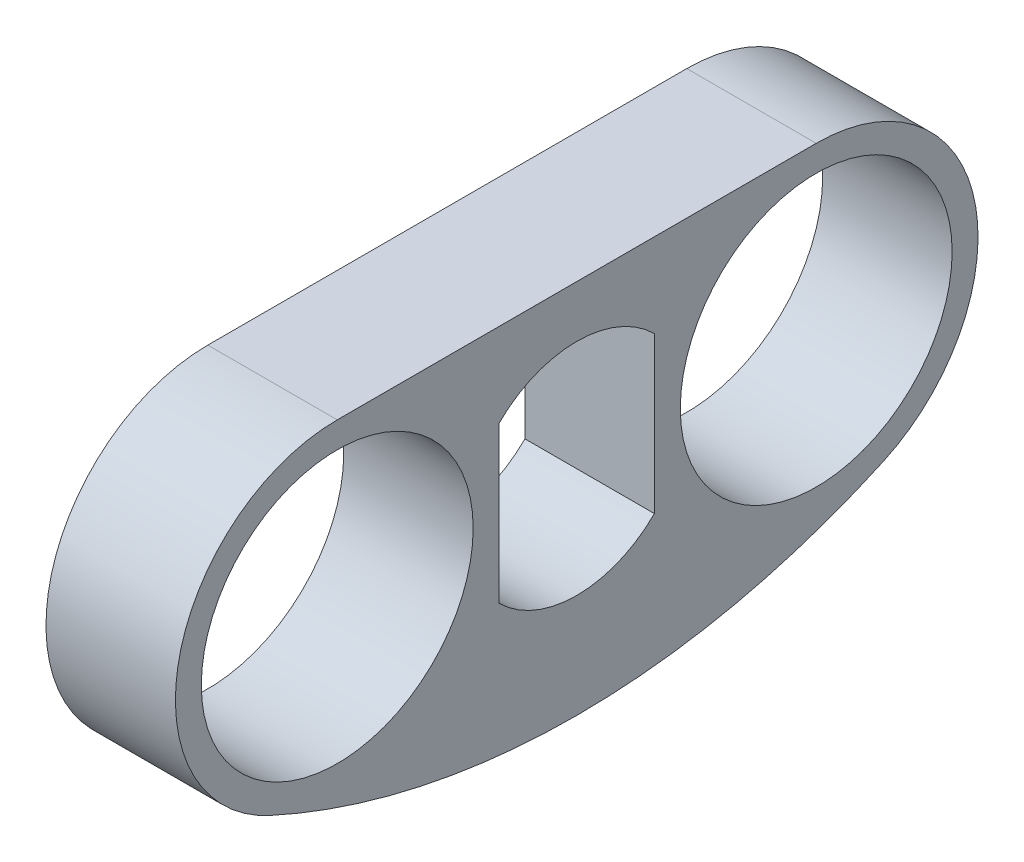
SolidWorks part; units mm, degrees
ref_plane "Alzado" through (0, 0, 0) normal (0, 0, 1) x (1, 0, 0)
ref_plane "Planta" through (0, 0, 0) normal (0, 1, 0) x (1, 0, 0)
ref_plane "Vista lateral" through (0, 0, 0) normal (1, 0, 0) x (0, 0, -1)
sketch "Croquis1" plane through (0, 0, 0) normal (1, 0, 0) x (0, 0, -1)
  line L0 (0, -8.5) -> (0, 8.5) construction
  line L15 (-6, -6.0208) -> (-6, 6.0208)
  line L17 (6, -6.0208) -> (6, 6.0208)
  line L18 (-6, -6.0208) -> (6, 6.0208) construction
  line L19 (-6, 6.0208) -> (6, -6.0208) construction
  line L20 (-7.5, -11) -> (7.5, -11) construction
  line L21 (-7.5, -11) -> (-7.5, 11) construction
  line L22 (-7.5, 11) -> (7.5, 11) construction
  line L23 (7.5, -11) -> (7.5, 11) construction
  line L24 (-18.5, 0) -> (18.5, 0) construction
  line L25 (-18.5, 12.5) -> (18.5, 12.5)
  arc A1 (-6, -6.0208) -> (6, -6.0208) centre (0, 0) ccw
  arc A2 (6, 6.0208) -> (-6, 6.0208) centre (0, 0) ccw
  circle A3 centre (18.5, 0) radius 10.5
  circle A4 centre (-18.5, 0) radius 10.5
  arc A5 (-18.5, 12.5) -> (-23.6966, -11.3686) centre (-18.5, 0) ccw
  arc A6 (23.6966, -11.3686) -> (18.5, 12.5) centre (18.5, 0) ccw
  arc A7 (-23.6966, -11.3686) -> (23.6966, -11.3686) centre (0, 40.4722) ccw
  point P10 (0, 11)
  point P11 (-7.5, 0)
  point P18 (0, 0)
  point P20 (0, 0)
  dimension "D3" = 15
  dimension "D1" = 17
  dimension "D5" = 21
  dimension "D7" = 12.5
  dimension "D8" = 114
  dimension "D10" = 12.5
  dimension "D2" = 12
  dimension "D4" = 22
  dimension "D6" = 11
  dimension "D9" = 37
  dimension "D11" = 27.9722
extrude "Saliente-Extruir1" add sketch "Croquis1" along normal blind 10
